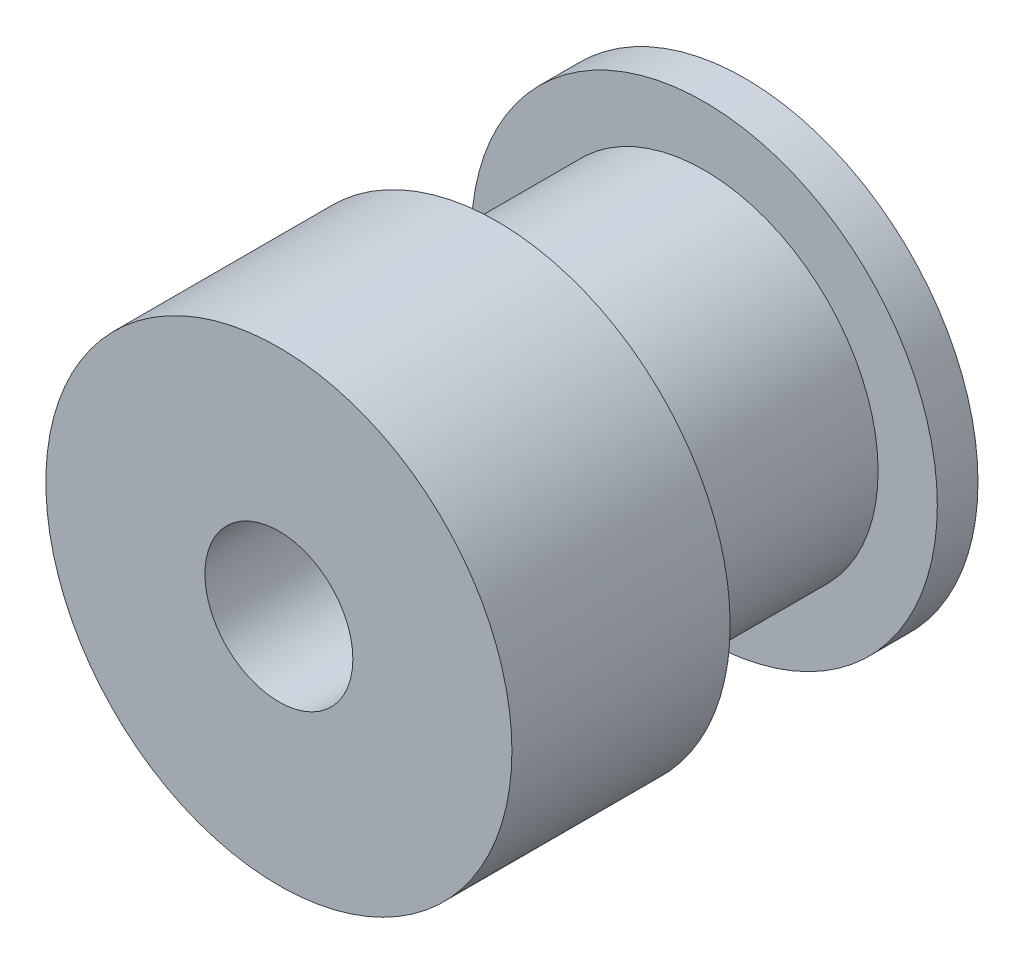
SolidWorks part; units mm, degrees
ref_plane "Front Plane" through (0, 0, 0) normal (0, 0, 1) x (1, 0, 0)
ref_plane "Top Plane" through (0, 0, 0) normal (0, 1, 0) x (1, 0, 0)
ref_plane "Right Plane" through (0, 0, 0) normal (1, 0, 0) x (0, 0, -1)
sketch "Sketch2" plane through (0, 0, 0) normal (0, 1, 0) x (1, 0, 0)
  line L0 (0, 0) -> (2.54, 0) construction
  line L1 (2.54, 0) -> (2.54, 16.002)
  line L2 (2.54, 16.002) -> (8.001, 16.002)
  line L3 (8.001, 16.002) -> (8.001, 14.605)
  line L4 (8.001, 14.605) -> (5.969, 14.605)
  line L5 (5.969, 14.605) -> (5.969, 7.493)
  line L6 (5.969, 7.493) -> (8.001, 7.493)
  line L7 (8.001, 7.493) -> (8.001, 0)
  line L8 (8.001, 0) -> (2.54, 0)
  line L9 (0, -0.1695) -> (0, 49999.8305) construction
  dimension "D1" = 7.493
  dimension "D2" = 2.54
  dimension "D3" = 7.112
  dimension "D4" = 1.397
  dimension "D5" = 5.461
  dimension "D6" = 2.032
revolve "Revolve1" add sketch "Sketch2" angle 360 about L9
sketch "Sketch4" plane through (0, 0, -16.002) normal (0, 0, -1) x (-1, 0, 0)
  point P0 (0, 0)
